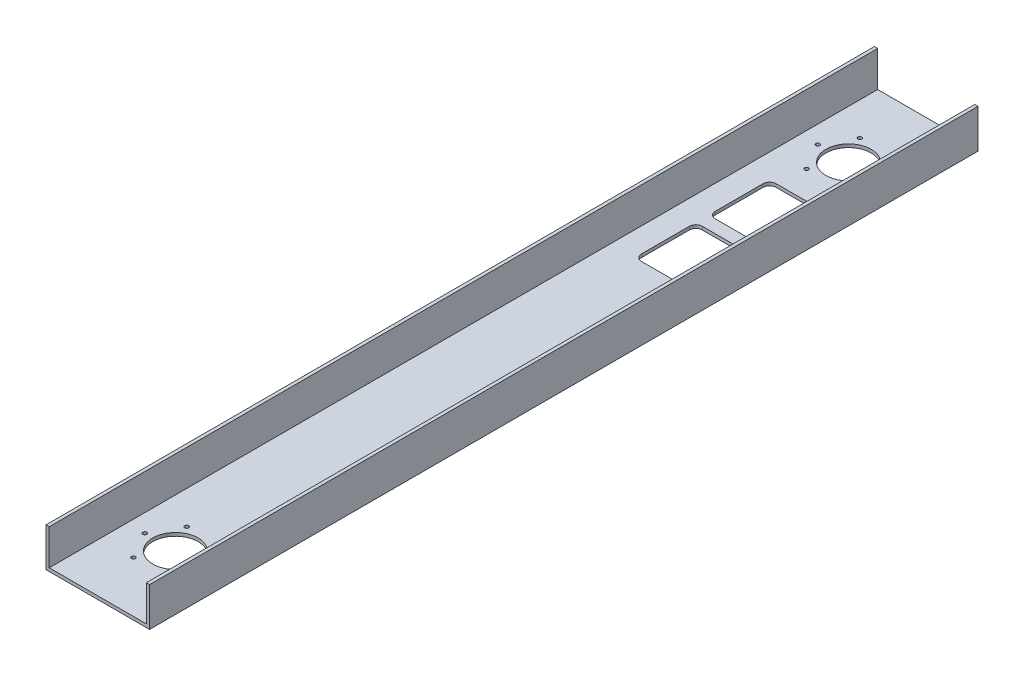
SolidWorks part; units mm, degrees
ref_plane "Front" through (0, 0, 0) normal (0, 0, 1) x (1, 0, 0)
ref_plane "Top" through (0, 0, 0) normal (0, 1, 0) x (1, 0, 0)
ref_plane "Right" through (0, 0, 0) normal (1, 0, 0) x (0, 0, -1)
sketch "Sketch1" plane through (0, 0, 0) normal (0, 0, 1) x (1, 0, 0)
  line L0 (3.175, 3.175) -> (3.175, 38.1)
  line L1 (0, 0) -> (101.6, 0)
  line L2 (0, 0) -> (0, 38.1)
  line L4 (101.6, 0) -> (101.6, 38.1)
  line L5 (3.175, 3.175) -> (98.425, 3.175)
  line L6 (98.425, 3.175) -> (98.425, 38.1)
  line L7 (0, 38.1) -> (3.175, 38.1)
  line L8 (101.6, 38.1) -> (98.425, 38.1)
  dimension "D1" = 38.1
  dimension "D2" = 101.6
  dimension "D3" = 3.175
extrude "Boss-Extrude1" add sketch "Sketch1" along normal blind 812.8
sketch "Sketch2" plane through (0, 0, 0) normal (0, -1, 0) x (1, 0, 0)
  line L0 (50.8, 812.8) -> (50.8, 736.6) construction
  line L1 (0, 812.8) -> (101.6, 812.8) construction
  circle A0 centre (50.8, 736.6) radius 22.2377
  dimension "D2" = 44.4754
  dimension "D1" = 76.2
extrude "Cut-Extrude1" cut sketch "Sketch2" against normal up to next (3.175 mm away)
sketch "Sketch3" plane through (0, 0, 0) normal (0, -1, 0) x (1, 0, 0)
  line L0 (50.8, 736.6) -> (65.8813, 762.7215) construction
  line L1 (65.8813, 762.7215) -> (35.7188, 762.7215) construction
  line L2 (50.8, 762.7215) -> (50.8, 736.6) construction
  circle A0 centre (65.8813, 762.7215) radius 1.8986
  circle A1 centre (80.9625, 736.6) radius 1.8987
  circle A2 centre (65.8813, 710.4785) radius 1.8986
  circle A3 centre (35.7188, 710.4785) radius 1.8986
  circle A4 centre (20.6375, 736.6) radius 1.8987
  circle A5 centre (35.7188, 762.7215) radius 1.8986
  circle A6 centre (50.8, 736.6) radius 22.2377 construction
  point P17 (50.8, 736.6)
  dimension "D2" = 3.7973
  dimension "D1" = 30.1625
  dimension "D3" = 6
extrude "Cut-Extrude2" cut sketch "Sketch3" against normal up to next (3.175 mm away)
ref_plane "Mid_Plane" through (0, 0, 406.4) normal (0, 0, 1) x (1, 0, 0)
mirror "Mirror1" about plane through (0, 0, 406.4) normal (0, 0, 1) of "Cut-Extrude2", "Cut-Extrude1"
sketch "Sketch4" plane through (0, 0, 0) normal (0, -1, 0) x (1, 0, 0)
  line L0 (26.9875, 149.3128) -> (0, 149.3128) construction
  line L3 (68.2625, 129.8363) -> (33.3375, 129.8363)
  line L4 (74.6125, 136.1863) -> (74.6125, 183.2)
  line L5 (68.2625, 261.9637) -> (33.3375, 261.9637)
  line L6 (26.9875, 136.1863) -> (26.9875, 183.2)
  line L7 (0, 812.8) -> (0, 0) construction
  line L8 (74.6125, 247.0656) -> (101.6, 247.0656) construction
  line L9 (101.6, 812.8) -> (101.6, 0) construction
  line L11 (33.3375, 189.55) -> (68.2625, 189.55)
  line L12 (33.3375, 202.25) -> (68.2625, 202.25)
  line L13 (26.9875, 208.6) -> (26.9875, 255.6137)
  line L14 (74.6125, 208.6) -> (74.6125, 255.6137)
  arc A0 (33.3375, 261.9637) -> (26.9875, 255.6137) centre (33.3375, 255.6137) ccw
  arc A1 (74.6125, 255.6137) -> (68.2625, 261.9637) centre (68.2625, 255.6137) ccw
  arc A2 (68.2625, 129.8363) -> (74.6125, 136.1863) centre (68.2625, 136.1863) ccw
  arc A3 (33.3375, 129.8363) -> (26.9875, 136.1863) centre (33.3375, 136.1863) cw
  arc A4 (33.3375, 202.25) -> (26.9875, 208.6) centre (33.3375, 208.6) cw
  arc A5 (68.2625, 202.25) -> (74.6125, 208.6) centre (68.2625, 208.6) ccw
  arc A6 (68.2625, 189.55) -> (74.6125, 183.2) centre (68.2625, 183.2) cw
  arc A7 (33.3375, 189.55) -> (26.9875, 183.2) centre (33.3375, 183.2) ccw
  dimension "D1" = 6.35
  dimension "D2" = 47.625
extrude "Cut-Extrude3" cut sketch "Sketch4" against normal up to next
